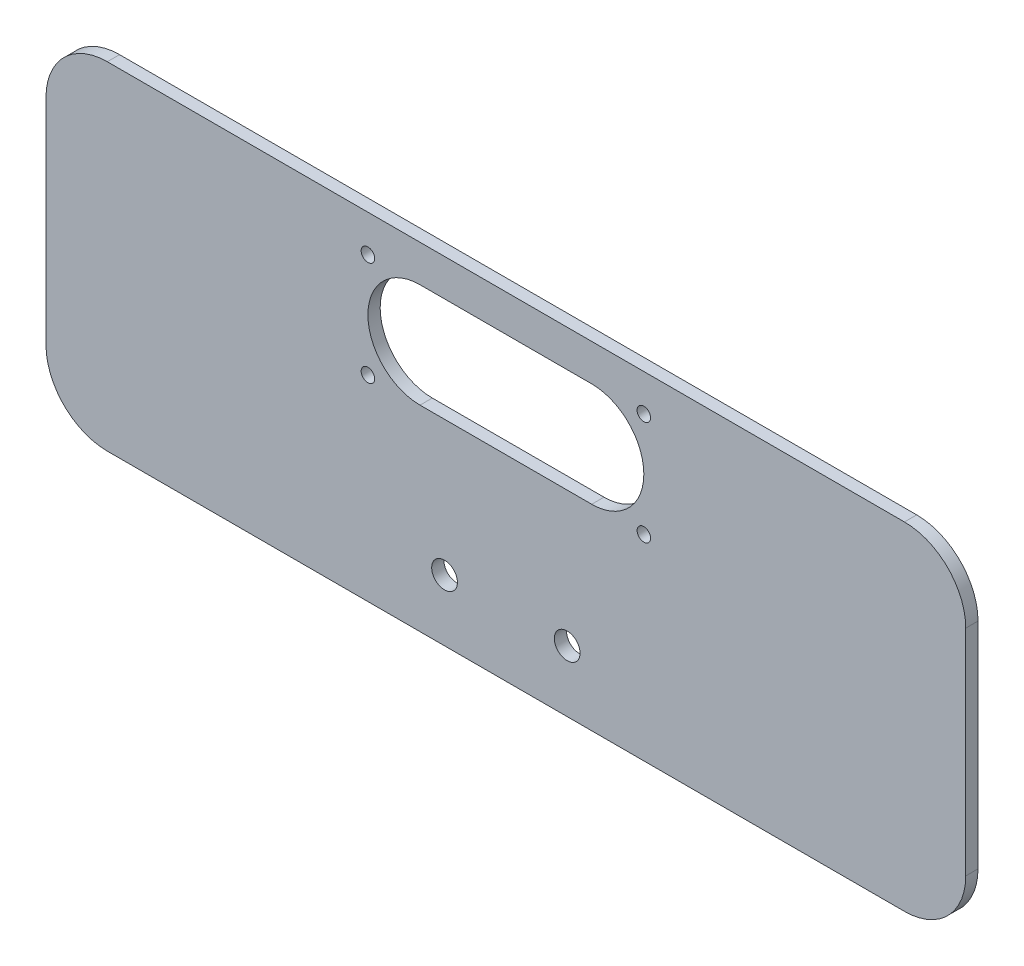
SolidWorks part; units mm, degrees
ref_plane "前视基准面" through (0, 0, 0) normal (0, 0, 1) x (1, 0, 0)
ref_plane "上视基准面" through (0, 0, 0) normal (0, 1, 0) x (1, 0, 0)
ref_plane "右视基准面" through (0, 0, 0) normal (1, 0, 0) x (0, 0, -1)
sketch "草图1" plane through (0, 0, 0) normal (0, 0, 1) x (1, 0, 0)
  line L0 (-75, -17.5) -> (75, -17.5) construction
  line L1 (-65, 27.5) -> (65, 27.5)
  line L2 (-75, 17.5) -> (-75, -17.5)
  line L3 (-65, -27.5) -> (65, -27.5)
  line L4 (75, 17.5) -> (75, -17.5)
  line L5 (0, -27.5) -> (0, 27.5) construction
  line L6 (-75, 0) -> (75, 0) construction
  line L7 (-22.4136, 13) -> (26.6488, 13) construction
  line L8 (-14, 13) -> (14, 13) construction
  line L9 (-14, 21.5) -> (14, 21.5)
  line L10 (-14, 4.5) -> (14, 4.5)
  line L11 (-22.5, 21.5) -> (-22.5, 4.5) construction
  circle A0 centre (-10, -17.5) radius 2.1
  arc A1 (-14, 21.5) -> (-14, 4.5) centre (-14, 13) ccw
  arc A2 (14, 4.5) -> (14, 21.5) centre (14, 13) ccw
  circle A3 centre (10, -17.5) radius 2.1
  arc A4 (65, -27.5) -> (75, -17.5) centre (65, -17.5) ccw
  arc A5 (65, 27.5) -> (75, 17.5) centre (65, 17.5) cw
  arc A6 (-75, -17.5) -> (-65, -27.5) centre (-65, -17.5) ccw
  arc A7 (-65, 27.5) -> (-75, 17.5) centre (-65, 17.5) ccw
  circle A8 centre (-22.5, 21.5) radius 1.1
  circle A9 centre (-22.5, 4.5) radius 1.1
  circle A10 centre (22.5, 4.5) radius 1.1
  circle A11 centre (22.5, 21.5) radius 1.1
  point P0 (0, 0)
  point P15 (0, 13)
  point P24 (75, -27.5)
  point P27 (75, 27.5)
  point P32 (-75, 27.5)
  point P35 (0, 0)
  point P37 (0, 0)
  dimension "D3" = 4.2
  dimension "D9" = 10
  dimension "D10" = 2.2
  dimension "D1" = 55
  dimension "D2" = 150
  dimension "D4" = 20
  dimension "D5" = 10
  dimension "D6" = 28
  dimension "D7" = 17
  dimension "D8" = 14.5
extrude "凸台-拉伸1" add sketch "草图1" along normal blind 2
